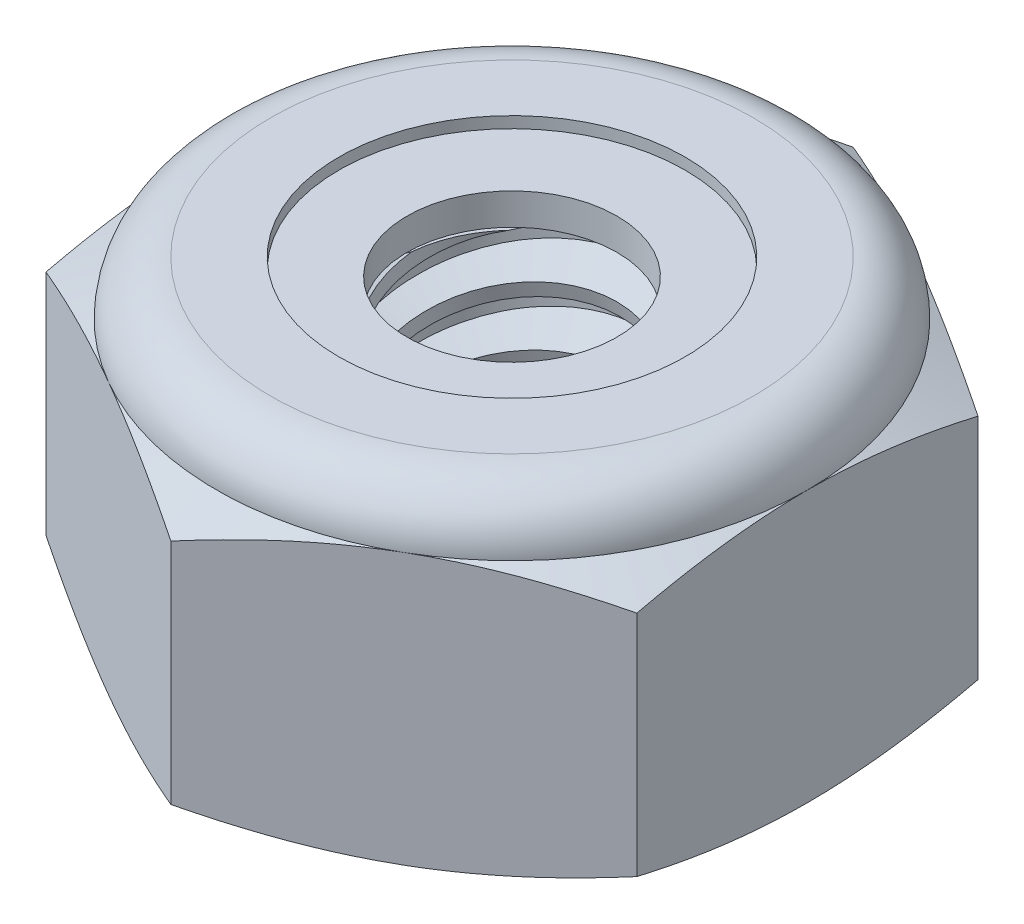
SolidWorks part; units mm, degrees
ref_plane "Front" through (0, 0, 0) normal (0, 0, 1) x (1, 0, 0)
ref_plane "Top" through (0, 0, 0) normal (0, 1, 0) x (1, 0, 0)
ref_plane "Right" through (0, 0, 0) normal (1, 0, 0) x (0, 0, -1)
sketch "Sketch1" plane through (0, 0, 0) normal (0, 1, 0) x (1, 0, 0)
  line L1 (0, 4.5827) -> (-3.9688, 2.2914)
  line L2 (-3.9688, 2.2914) -> (-3.9688, -2.2914)
  line L3 (-3.9688, -2.2914) -> (0, -4.5827)
  line L4 (0, -4.5827) -> (3.9688, -2.2914)
  line L5 (3.9688, -2.2914) -> (3.9687, 2.2914)
  line L6 (3.9687, 2.2914) -> (0, 4.5827)
  circle A0 centre (0, 0) radius 3.9688 construction
  dimension "Hex Flats" = 7.9375
extrude "Extrude1" add sketch "Sketch1" along normal blind 4.3656
sketch "Sketch2" plane through (0, 0, 0) normal (1, 0, 0) x (0, 0, -1)
  line L0 (-1.7526, 0) -> (-1.7526, 4.3656) construction
  line L1 (0, 0) -> (1.7526, 0)
  line L2 (0, 0) -> (0, 4.3656)
  line L3 (0, 4.3656) -> (1.7526, 4.3656)
  line L4 (1.7526, 0) -> (1.7526, 4.3656)
  line L5 (-2.2914, 4.3656) -> (2.2914, 4.3656) construction
  line L7 (0, -1.7526) -> (0, 0) construction
  dimension "Thread Dia" = 3.5052
revolve "Revolve1" add sketch "Sketch2" angle 360 about L7
sketch "Sketch3" plane through (0, 0, 0) normal (1, 0, 0) x (0, 0, -1)
  line L0 (1.7526, 4.3656) -> (-1.7526, 4.3656) construction
  line L1 (-1.7526, 4.3656) -> (-1.7526, 3.5719) construction
  line L2 (-1.7526, 3.5719) -> (1.7526, 4.3656) construction
  line L3 (1.7526, 4.3656) -> (1.7745, 4.2689) construction
  line L4 (1.7745, 4.2689) -> (1.9279, 3.5915)
  line L5 (1.9279, 3.5915) -> (1.4541, 3.7385)
  line L6 (1.4541, 3.7385) -> (1.4103, 3.932)
  line L7 (1.4103, 3.932) -> (1.7745, 4.2689)
  line L8 (1.4322, 3.8353) -> (1.8512, 3.9302) construction
  line L9 (1.7526, 4.3656) -> (1.7526, 3.9078) construction
  line L10 (1.7526, 3.9078) -> (-1.7526, 3.1141) construction
  line L11 (-1.7526, 3.1141) -> (-1.7526, 3.5719) construction
  line L12 (-0.1935, 4.3656) -> (0.1935, 2.6563) construction
  line L13 (-1.7526, 0) -> (-1.7526, 4.3656) construction
  line L14 (0, 4.3656) -> (1.7526, 4.3656) construction
  line L15 (1.7526, 0) -> (1.7526, 4.3656) construction
  point P13 (0, 3.511)
  dimension "D1" = 0.0992
  dimension "D2" = 0.1984
  dimension "Thread Pitch" = 0.7937
  dimension "D4" = 60
  dimension "D5" = 0.7937
revolve "Cut-Revolve1" cut sketch "Sketch3" angle 360 about L12
pattern_linear "LPattern1" count 6 spacing 0.7937 along (0, -1, 0) count 2 spacing 0.7937 along (0, 1, 0) of "Cut-Revolve1"
sketch "Sketch4" plane through (0, 0, 0) normal (1, 0, 0) x (0, 0, -1)
  line L0 (0, 4.3656) -> (1.7526, 4.3656)
  line L1 (1.7526, 4.3656) -> (1.4103, 4.206)
  line L2 (1.4103, 4.206) -> (1.4103, 0.1596)
  line L3 (1.4103, 0.1596) -> (1.7526, 0)
  line L4 (1.7526, 0) -> (0, 0)
  line L5 (0, 0) -> (0, 4.3656)
  line L6 (1.7526, 0) -> (1.7526, 4.3656) construction
  line L7 (0, 4.3656) -> (1.7526, 4.3656) construction
  line L8 (0, 0) -> (1.7526, 0) construction
  line L9 (0, 0) -> (0, 4.3656) construction
  line L10 (0, 4.3656) -> (0, 4.7433) construction
  dimension "D1" = 25
revolve "Cut-Revolve2" cut sketch "Sketch4" angle 360 about L10
combine bodies "Combine1" operation type subtract main body 112 bodies to subtract 111
sketch "Sketch5" plane through (0, 0, 0) normal (1, 0, 0) x (0, 0, -1)
  line L0 (0, 0) -> (3.9688, 0)
  line L1 (3.9688, 0) -> (4.5827, 0.2863)
  line L2 (4.5827, 0.2863) -> (4.5827, 3.3517)
  line L3 (4.5827, 3.3517) -> (3.9687, 3.638)
  line L4 (3.2411, 4.3656) -> (3.2411, 5.6356)
  line L5 (3.2411, 5.6356) -> (5.8527, 5.6356)
  line L6 (5.8527, 5.6356) -> (5.8527, -1.27)
  line L7 (5.8527, -1.27) -> (0, -1.27)
  line L8 (0, -1.27) -> (0, 0)
  line L9 (3.9687, 3.638) -> (3.9688, 0) construction
  line L10 (0, 0) -> (1.7526, 0) construction
  line L13 (4.5827, 1.819) -> (5.8527, 1.819) construction
  line L14 (4.5827, 4.3656) -> (4.5827, 0) construction
  line L15 (0, 0) -> (0, 5.6356) construction
  line L20 (0, 5.6356) -> (3.2411, 5.6356) construction
  line L22 (0, 4.3656) -> (1.7526, 4.3656) construction
  arc A0 (3.9687, 3.638) -> (3.2411, 4.3656) centre (3.2411, 3.638) ccw
  dimension "D1" = 25
  dimension "D2" = 1.27
  dimension "D3" = 4.3656
  dimension "D4" = 0.7276
revolve "Cut-Revolve3" cut sketch "Sketch5" angle 360 about L15
sketch "Sketch6" plane through (0, 0, 0) normal (1, 0, 0) x (0, 0, -1)
  line L0 (0, 3.638) -> (3.8163, 3.638)
  line L1 (3.2411, 4.2132) -> (2.3257, 4.2132)
  line L2 (0, 5.6356) -> (0, 3.638)
  line L3 (2.3257, 5.6356) -> (0, 5.6356)
  line L4 (0, 5.6356) -> (3.2411, 5.6356) construction
  line L5 (0, 0) -> (0, 5.6356) construction
  line L6 (0, 5.6356) -> (0, 44.323) construction
  line L7 (2.3257, 4.2132) -> (2.3257, 5.6356)
  line L8 (3.2411, 4.3656) -> (3.2411, 4.2132) construction
  line L9 (2.3257, 4.2132) -> (1.4103, 4.2132) construction
  line L10 (1.4103, 4.2132) -> (1.4103, 4.206) construction
  arc A0 (3.8163, 3.638) -> (3.2411, 4.2132) centre (3.2411, 3.638) ccw
  arc A1 (3.9687, 3.638) -> (3.2411, 4.3656) centre (3.2411, 3.638) ccw construction
  dimension "D1" = 0.1524
revolve "Cut-Revolve4" cut sketch "Sketch6" angle 360 about L6
sketch "Sketch7" plane through (0, 0, 0) normal (1, 0, 0) x (0, 0, -1)
  line L0 (1.4103, 3.7142) -> (3.7343, 3.7142)
  line L1 (3.2411, 4.137) -> (1.4103, 4.137)
  line L2 (1.4103, 4.137) -> (1.4103, 3.7142)
  line L3 (1.4103, 3.7142) -> (0, 3.7142) construction
  line L4 (0, 3.7142) -> (0, 4.137) construction
  line L5 (0, 4.137) -> (1.4103, 4.137) construction
  line L6 (1.4103, 3.7142) -> (1.4103, 3.638) construction
  line L7 (0, 3.638) -> (3.8163, 3.638) construction
  line L8 (3.2411, 4.137) -> (3.2411, 4.2132) construction
  arc A0 (3.7343, 3.7142) -> (3.2411, 4.137) centre (3.2411, 3.638) ccw
  arc A2 (3.8163, 3.638) -> (3.2411, 4.2132) centre (3.2411, 3.638) ccw construction
  dimension "D1" = 0.0762
revolve "Revolve2" add sketch "Sketch7" angle 360 about L4
equation "\"D1@Sketch3\"=\"Thread Pitch@Sketch3\"/8"
equation "\"D2@Sketch3\"=\"Thread Pitch@Sketch3\"/4"
equation "\"D5@Sketch3\"=\"Thread Pitch@Sketch3\""
equation "\"D4@LPattern1\"=\"Thread Pitch@Sketch3\""
equation "\"D3@LPattern1\"=\"Thread Pitch@Sketch3\""
equation "\"D1@LPattern1\"=\"Height@Extrude1\"/\"Thread Pitch@Sketch3\""
equation "\"D4@Sketch5\"=\"Height@Extrude1\"/6"
